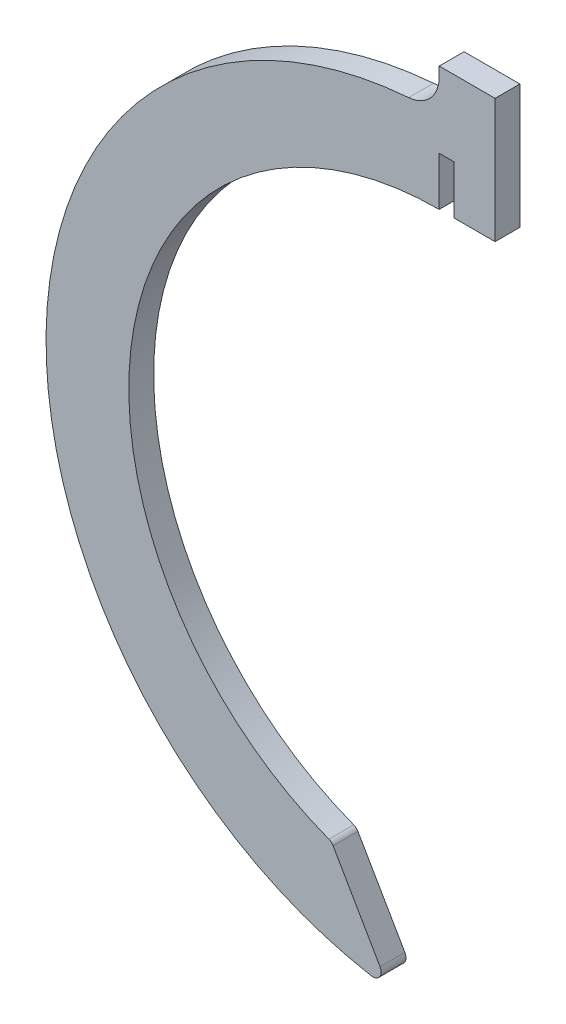
SolidWorks part; units mm, degrees
ref_plane "Front Plane" through (0, 0, 0) normal (0, 0, 1) x (1, 0, 0)
ref_plane "Top Plane" through (0, 0, 0) normal (0, 1, 0) x (1, 0, 0)
ref_plane "Right Plane" through (0, 0, 0) normal (1, 0, 0) x (0, 0, -1)
sketch "Sketch1" plane through (0, 0, 0) normal (0, 0, 1) x (1, 0, 0)
  line L0 (0, 43.3767) -> (0, 37.5)
  line L1 (-12.9954, -35.1763) -> (-6.108, -47.1057)
  line L2 (-6.108, -47.1057) -> (-67.2696, -47.1057) construction
  line L3 (0, 47.5) -> (0, 52.5)
  line L4 (0, 52.5) -> (6.75, 52.5)
  line L5 (1.79, 37.5) -> (6.75, 37.5)
  line L6 (6.75, 37.5) -> (6.75, 52.5)
  line L7 (0, 43.3767) -> (1.79, 43.3767)
  line L8 (1.79, 43.3767) -> (1.79, 37.5)
  arc A0 (0, 37.5) -> (-12.9954, -35.1763) centre (0, 0) ccw
  arc A1 (0, 47.5) -> (-6.108, -47.1057) centre (0, 0) ccw
  dimension "D1" = 75
  dimension "D2" = 10
  dimension "D3" = 60
  dimension "D4" = 15
  dimension "D5" = 5
  dimension "D6" = 6.75
  dimension "D7" = 4.96
  dimension "D8" = 1.79
extrude "Boss-Extrude1" add sketch "Sketch1" along normal blind 3
fillet "Fillet1" radius 4 1 edges at (0, 47.5, 1.5)
fillet "Fillet2" radius 1 1 edges at (-12.9954, -35.1763, 1.5)
fillet "Fillet3" radius 1 1 edges at (-6.108, -47.1057, 1.5)
